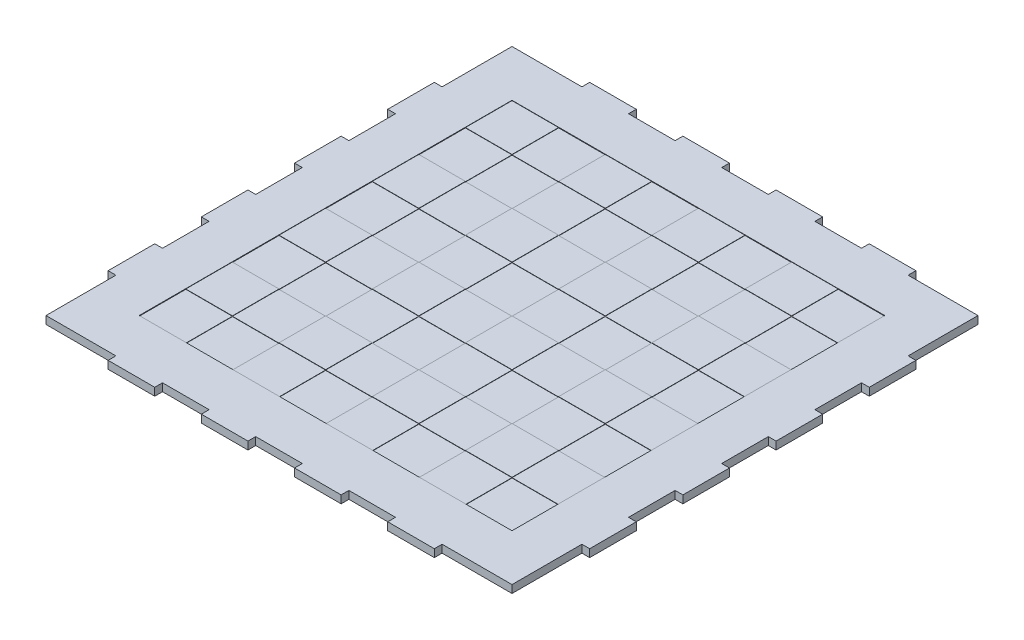
SolidWorks part; units mm, degrees
ref_plane "Plan de face" through (0, 0, 0) normal (0, 0, 1) x (1, 0, 0)
ref_plane "Plan de dessus" through (0, 0, 0) normal (0, 1, 0) x (1, 0, 0)
ref_plane "Plan de droite" through (0, 0, 0) normal (1, 0, 0) x (0, 0, -1)
sketch "Esquisse1" plane through (0, 0, 0) normal (0, 1, 0) x (1, 0, 0)
  line L4 (-190.5, -190.5) -> (190.5, -190.5)
  line L5 (190.5, 190.5) -> (190.5, -190.5)
  line L44 (-190.5, -190.5) -> (-190.5, 190.5)
  line L45 (-190.5, 190.5) -> (190.5, 190.5)
  point P0 (0, 190.5)
  point P6 (190.5, 0)
  dimension "D1" = 381
  dimension "D2" = 381
extrude "Boss.-Extru.1" add sketch "Esquisse1" along normal blind 6.35
sketch "Esquisse2" plane through (190.5, 0, 0) normal (1, 0, 0) x (0, 0, -1)
  line L0 (-190.5, 6.35) -> (190.5, 6.35) construction
  line L1 (-133.35, 6.35) -> (-95.25, 6.35)
  line L2 (-133.35, 6.35) -> (-133.35, 0)
  line L3 (-133.35, 0) -> (-95.25, 0)
  line L4 (-95.25, 6.35) -> (-95.25, 0)
  line L5 (-190.5, 0) -> (190.5, 0) construction
  line L6 (-190.5, 6.35) -> (-190.5, 0) construction
  dimension "D1" = 38.1
  dimension "D2" = 57.15
extrude "Boss.-Extru.2" add sketch "Esquisse2" along normal blind 6.35
pattern_linear "Répétition linéaire1" count 4 spacing 76.2 along (0, 0, -1) of "Boss.-Extru.2"
mirror "Symétrie1" about plane through (0, 0, 0) normal (1, 0, 0) of "Répétition linéaire1", "Boss.-Extru.2"
sketch "Esquisse3" plane through (0, 0, 190.5) normal (0, 0, 1) x (1, 0, 0)
  line L0 (-190.5, 6.35) -> (190.5, 6.35) construction
  line L1 (133.35, 6.35) -> (95.25, 6.35)
  line L2 (133.35, 6.35) -> (133.35, 0)
  line L3 (133.35, 0) -> (95.25, 0)
  line L4 (95.25, 6.35) -> (95.25, 0)
  line L5 (-190.5, 0) -> (190.5, 0) construction
  line L6 (190.5, 6.35) -> (190.5, 0) construction
  dimension "D1" = 38.1
  dimension "D2" = 57.15
extrude "Boss.-Extru.3" add sketch "Esquisse3" along normal blind 6.35
pattern_linear "Répétition linéaire2" count 4 spacing 76.2 along (-1, 0, 0) of "Boss.-Extru.3"
mirror "Symétrie2" about plane through (0, 0, 0) normal (0, 0, 1) of "Répétition linéaire2", "Boss.-Extru.3"
sketch "Esquisse10" plane through (0, 6.35, 0) normal (0, 1, 0) x (1, 0, 0)
  line L1 (-152.4, 152.4) -> (152.4, 152.4)
  line L2 (-152.4, 152.4) -> (-152.4, -152.4)
  line L3 (-152.4, -152.4) -> (152.4, -152.4)
  line L4 (152.4, 152.4) -> (152.4, -152.4)
  point P4 (152.4, 0)
  point P6 (0, 152.4)
  dimension "D1" = 304.8
  dimension "D2" = 304.8
extrude "Enlèv. mat.-Extru.3" cut sketch "Esquisse10" against normal blind 0.508
sketch "Esquisse11" plane through (0, 5.842, 0) normal (0, 1, 0) x (1, 0, 0)
  line L1 (-152.4, 152.4) -> (-114.3, 152.4)
  line L2 (-152.4, 152.4) -> (-152.4, 114.3)
  line L3 (-152.4, 114.3) -> (-114.3, 114.3)
  line L4 (-114.3, 152.4) -> (-114.3, 114.3)
  dimension "D1" = 38.1
  dimension "D2" = 38.1
extrude "Boss.-Extru.5" add sketch "Esquisse11" along normal blind 0.254
pattern_linear "Répétition linéaire3" count 4 spacing 76.2 along (0, 0, 1) count 4 spacing 76.2 along (1, 0, 0) of "Boss.-Extru.5"
sketch "Esquisse12" plane through (0, 5.842, 0) normal (0, 1, 0) x (1, 0, 0)
  line L1 (-114.3, 114.3) -> (-76.2, 114.3)
  line L2 (-114.3, 114.3) -> (-114.3, 76.2)
  line L3 (-114.3, 76.2) -> (-76.2, 76.2)
  line L4 (-76.2, 114.3) -> (-76.2, 76.2)
extrude "Enlèv. mat.-Extru.4" cut sketch "Esquisse12" against normal blind 0.254
pattern_linear "Répétition linéaire4" count 4 spacing 76.2 along (0, 0, 1) count 4 spacing 76.2 along (1, 0, 0) of "Enlèv. mat.-Extru.4"
